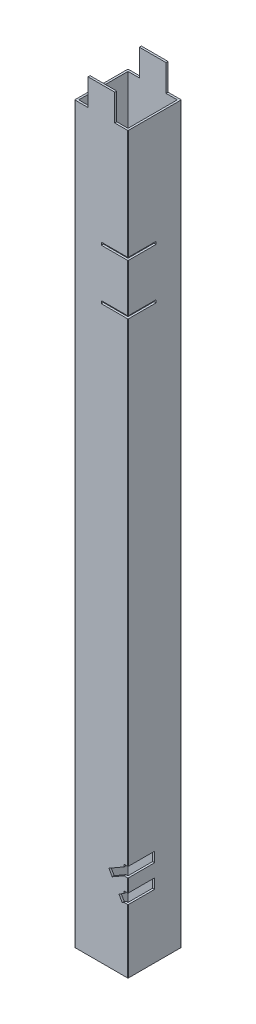
SolidWorks part; units mm, degrees
ref_plane "Front Plane" through (0, 0, 0) normal (0, 0, 1) x (1, 0, 0)
ref_plane "Top Plane" through (0, 0, 0) normal (0, 1, 0) x (1, 0, 0)
ref_plane "Right Plane" through (0, 0, 0) normal (1, 0, 0) x (0, 0, -1)
sketch "Sketch1" plane through (0, 0, 0) normal (0, 1, 0) x (1, 0, 0)
  line L0 (1.5, 1.5) -> (38.5, 1.5)
  line L1 (0.5, 0) -> (39.5, 0)
  line L2 (0, 0.5) -> (0, 39.5)
  line L3 (0.5, 40) -> (39.5, 40)
  line L4 (40, 0.5) -> (40, 39.5)
  line L5 (38.5, 1.5) -> (38.5, 38.5)
  line L6 (1.5, 38.5) -> (38.5, 38.5)
  line L7 (1.5, 1.5) -> (1.5, 38.5)
  arc A0 (39.5, 0) -> (40, 0.5) centre (39.5, 0.5) ccw
  arc A1 (0.5, 0) -> (0, 0.5) centre (0.5, 0.5) cw
  arc A2 (0, 39.5) -> (0.5, 40) centre (0.5, 39.5) cw
  arc A3 (39.5, 40) -> (40, 39.5) centre (39.5, 39.5) cw
  arc A4 (38.5, 1.5) -> (38.5, 1.5) centre (38.5, 1.5) ccw
  arc A5 (38.5, 38.5) -> (38.5, 38.5) centre (38.5, 38.5) cw
  arc A6 (1.5, 38.5) -> (1.5, 38.5) centre (1.5, 38.5) cw
  arc A7 (1.5, 1.5) -> (1.5, 1.5) centre (1.5, 1.5) cw
  point P9 (0, 0)
  dimension "D3" = 0.5
  dimension "D1" = 40
  dimension "D2" = 40
  dimension "D4" = 1.5
extrude "Boss-Extrude1" add sketch "Sketch1" along normal blind 571
sketch "Sketch2" plane through (0, 0, -40) normal (0, 0, 1) x (1, 0, 0)
  line L0 (0.5, 571) -> (39.5, 571) construction
  line L11 (30, 571) -> (40, 571)
  line L12 (30, 571) -> (30, 551)
  line L13 (30, 551) -> (40, 551)
  line L14 (40, 571) -> (40, 551)
  line L15 (40, 571) -> (40, 0) construction
  line L16 (20, 571) -> (20, 1571.1839) construction
  line L17 (0, 571) -> (0, 551)
  line L18 (10, 551) -> (0, 551)
  line L19 (10, 571) -> (10, 551)
  line L20 (10, 571) -> (0, 571)
  dimension "D1" = 20
  dimension "D2" = 10
extrude "Cut-Extrude1" cut sketch "Sketch2" along normal blind 40
sketch "Sketch3" plane through (40, 0, 0) normal (1, 0, 0) x (0, 0, -1)
  line L6 (0, 551) -> (0, 0) construction
  line L12 (21, 468.5) -> (0, 468.5)
  line L13 (21, 468.5) -> (21, 466.5)
  line L14 (21, 466.5) -> (0, 466.5)
  line L15 (0, 468.5) -> (0, 466.5)
  line L16 (0.5, 551) -> (39.5, 551) construction
  line L17 (0, 448.5) -> (12.9815, 448.5) construction
  line L18 (0, 428.5) -> (0, 430.5)
  line L19 (21, 430.5) -> (0, 430.5)
  line L20 (21, 428.5) -> (21, 430.5)
  line L21 (21, 428.5) -> (0, 428.5)
  dimension "D1" = 2
  dimension "D2" = 21
  dimension "D3" = 82.5
  dimension "D4" = 20
extrude "Cut-Extrude2" cut sketch "Sketch3" against normal blind 20
sketch "Sketch4" plane through (0, 0, -40) normal (0, 0, -1) x (-1, 0, 0)
  line L0 (-40, 72.5999) -> (-37, 72.5999)
  line L5 (-25.6597, 64.3205) -> (-346.4, 249.5) construction
  line L7 (-37, 72.5999) -> (-37, 70.8678)
  line L8 (-37, 70.8678) -> (-25.6597, 64.3205)
  line L9 (-25.6597, 64.3205) -> (-28.1597, 59.9904)
  line L11 (-28.1597, 59.9904) -> (-37, 65.0943)
  line L13 (-37, 65.0943) -> (-40, 65.0943)
  line L16 (-40, 551) -> (-40, 0) construction
  line L19 (-40, 65.0943) -> (-40, 72.5999)
  line L30 (-37, 70.8678) -> (-40, 72.5999) construction
  line L32 (-40, 72.5999) -> (-41.208, 73.2973) construction
  line L36 (-28.1597, 59.9904) -> (-41.1501, 67.4904) construction
  line L38 (-25.9097, 63.8875) -> (-28.1597, 59.9904) construction
  line L49 (-40, 55.2794) -> (-37, 55.2794)
  line L50 (-41.1501, 55.9434) -> (-33.1597, 51.3301) construction
  line L51 (-37, 55.2794) -> (-37, 53.5473)
  line L52 (-37, 53.5473) -> (-33.1597, 51.3301)
  line L55 (-39.5, 551) -> (-39.5, 0) construction
  line L56 (-37, 47.7738) -> (-40, 47.7738)
  line L57 (-40, 47.7738) -> (-40, 55.2794)
  line L58 (-40, 49.5059) -> (-35.6597, 47) construction
  line L59 (-35.6597, 47) -> (-386.4, 249.5) construction
  line L60 (-37, 47.7738) -> (-35.6597, 47)
  line L61 (-35.6597, 47) -> (-33.1597, 51.3301)
  line L62 (-39.5, 0) -> (-0.5, 0) construction
  dimension "D1" = 3
  dimension "D2" = 3
  dimension "D3" = 3
  dimension "D4" = 3
  dimension "D5" = 6.8403
  dimension "D6" = 47.7738
extrude "Cut-Extrude3" cut sketch "Sketch4" along normal blind 20 from offset 40 offset against normal yes
sketch "Sketch5" plane through (0, 0, -40) normal (0, 0, -1) x (-1, 0, 0)
  line L0 (-39.5, 0) -> (-0.5, 0) construction
  line L1 (-40, 551) -> (-40, 0) construction
  circle A0 centre (-30, 15) radius 3.5
  circle A1 centre (-30, 30) radius 3.5
  point P4 (0, 0)
  dimension "D1" = 7
  dimension "D3" = 15
  dimension "D4" = 10
  dimension "D2" = 15
extrude "Cut-Extrude4" cut sketch "Sketch5" against normal blind 10
